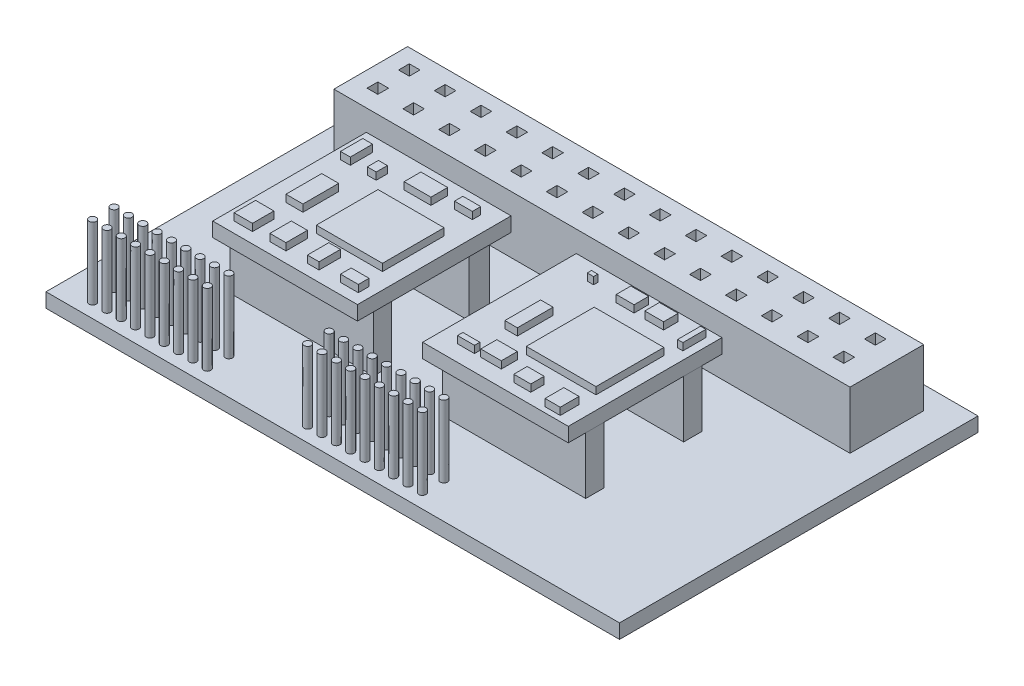
SolidWorks part; units mm, degrees
ref_plane "前视基准面" through (0, 0, 0) normal (0, 0, 1) x (1, 0, 0)
ref_plane "上视基准面" through (0, 0, 0) normal (0, 1, 0) x (1, 0, 0)
ref_plane "右视基准面" through (0, 0, 0) normal (1, 0, 0) x (0, 0, -1)
sketch "草图1" plane through (0, 0, 0) normal (0, 1, 0) x (1, 0, 0)
  line L1 (0, 50) -> (80, 50)
  line L2 (0, 50) -> (0, 0)
  line L3 (0, 0) -> (80, 0)
  line L4 (80, 50) -> (80, 0)
  dimension "D1" = 80
  dimension "D2" = 50
extrude "凸台-拉伸1" add sketch "草图1" along normal blind 2
sketch "草图2" plane through (0, 2, 0) normal (0, 1, 0) x (1, 0, 0)
  line L0 (10.7958, 38.9843) -> (12.2958, 38.9843)
  line L1 (3.6003, 46.8398) -> (75.5909, 46.8398)
  line L2 (3.6003, 46.8398) -> (3.6003, 36.5555)
  line L3 (3.6003, 36.5555) -> (75.5909, 36.5555)
  line L4 (75.5909, 46.8398) -> (75.5909, 36.5555)
  line L5 (5.7958, 44.8754) -> (7.2958, 44.8754)
  line L6 (5.7958, 44.8754) -> (5.7958, 43.3754)
  line L7 (5.7958, 43.3754) -> (7.2958, 43.3754)
  line L8 (7.2958, 44.8754) -> (7.2958, 43.3754)
  line L9 (5.7958, 40.4843) -> (7.2958, 40.4843)
  line L10 (5.7958, 40.4843) -> (5.7958, 38.9843)
  line L11 (5.7958, 38.9843) -> (7.2958, 38.9843)
  line L12 (7.2958, 40.4843) -> (7.2958, 38.9843)
  line L13 (10.7958, 40.4843) -> (10.7958, 38.9843)
  line L14 (10.7958, 40.4843) -> (12.2958, 40.4843)
  line L15 (12.2958, 40.4843) -> (12.2958, 38.9843)
  line L16 (10.7958, 43.3754) -> (12.2958, 43.3754)
  line L17 (12.2958, 44.8754) -> (12.2958, 43.3754)
  line L18 (10.7958, 44.8754) -> (12.2958, 44.8754)
  line L19 (10.7958, 44.8754) -> (10.7958, 43.3754)
  line L20 (15.7958, 38.9843) -> (17.2958, 38.9843)
  line L21 (15.7958, 40.4843) -> (15.7958, 38.9843)
  line L22 (15.7958, 40.4843) -> (17.2958, 40.4843)
  line L23 (17.2958, 40.4843) -> (17.2958, 38.9843)
  line L24 (15.7958, 43.3754) -> (17.2958, 43.3754)
  line L25 (17.2958, 44.8754) -> (17.2958, 43.3754)
  line L26 (15.7958, 44.8754) -> (17.2958, 44.8754)
  line L27 (15.7958, 44.8754) -> (15.7958, 43.3754)
  line L28 (20.7958, 38.9843) -> (22.2958, 38.9843)
  line L29 (20.7958, 40.4843) -> (20.7958, 38.9843)
  line L30 (20.7958, 40.4843) -> (22.2958, 40.4843)
  line L31 (22.2958, 40.4843) -> (22.2958, 38.9843)
  line L32 (20.7958, 43.3754) -> (22.2958, 43.3754)
  line L33 (22.2958, 44.8754) -> (22.2958, 43.3754)
  line L34 (20.7958, 44.8754) -> (22.2958, 44.8754)
  line L35 (20.7958, 44.8754) -> (20.7958, 43.3754)
  line L36 (25.7958, 38.9843) -> (27.2958, 38.9843)
  line L37 (25.7958, 40.4843) -> (25.7958, 38.9843)
  line L38 (25.7958, 40.4843) -> (27.2958, 40.4843)
  line L39 (27.2958, 40.4843) -> (27.2958, 38.9843)
  line L40 (25.7958, 43.3754) -> (27.2958, 43.3754)
  line L41 (27.2958, 44.8754) -> (27.2958, 43.3754)
  line L42 (25.7958, 44.8754) -> (27.2958, 44.8754)
  line L43 (25.7958, 44.8754) -> (25.7958, 43.3754)
  line L44 (30.7958, 38.9843) -> (32.2958, 38.9843)
  line L45 (30.7958, 40.4843) -> (30.7958, 38.9843)
  line L46 (30.7958, 40.4843) -> (32.2958, 40.4843)
  line L47 (32.2958, 40.4843) -> (32.2958, 38.9843)
  line L48 (30.7958, 43.3754) -> (32.2958, 43.3754)
  line L49 (32.2958, 44.8754) -> (32.2958, 43.3754)
  line L50 (30.7958, 44.8754) -> (32.2958, 44.8754)
  line L51 (30.7958, 44.8754) -> (30.7958, 43.3754)
  line L52 (35.7958, 38.9843) -> (37.2958, 38.9843)
  line L53 (35.7958, 40.4843) -> (35.7958, 38.9843)
  line L54 (35.7958, 40.4843) -> (37.2958, 40.4843)
  line L55 (37.2958, 40.4843) -> (37.2958, 38.9843)
  line L56 (35.7958, 43.3754) -> (37.2958, 43.3754)
  line L57 (37.2958, 44.8754) -> (37.2958, 43.3754)
  line L58 (35.7958, 44.8754) -> (37.2958, 44.8754)
  line L59 (35.7958, 44.8754) -> (35.7958, 43.3754)
  line L60 (40.7958, 38.9843) -> (42.2958, 38.9843)
  line L61 (40.7958, 40.4843) -> (40.7958, 38.9843)
  line L62 (40.7958, 40.4843) -> (42.2958, 40.4843)
  line L63 (42.2958, 40.4843) -> (42.2958, 38.9843)
  line L64 (40.7958, 43.3754) -> (42.2958, 43.3754)
  line L65 (42.2958, 44.8754) -> (42.2958, 43.3754)
  line L66 (40.7958, 44.8754) -> (42.2958, 44.8754)
  line L67 (40.7958, 44.8754) -> (40.7958, 43.3754)
  line L68 (45.7958, 38.9843) -> (47.2958, 38.9843)
  line L69 (45.7958, 40.4843) -> (45.7958, 38.9843)
  line L70 (45.7958, 40.4843) -> (47.2958, 40.4843)
  line L71 (47.2958, 40.4843) -> (47.2958, 38.9843)
  line L72 (45.7958, 43.3754) -> (47.2958, 43.3754)
  line L73 (47.2958, 44.8754) -> (47.2958, 43.3754)
  line L74 (45.7958, 44.8754) -> (47.2958, 44.8754)
  line L75 (45.7958, 44.8754) -> (45.7958, 43.3754)
  line L76 (50.7958, 38.9843) -> (52.2958, 38.9843)
  line L77 (50.7958, 40.4843) -> (50.7958, 38.9843)
  line L78 (50.7958, 40.4843) -> (52.2958, 40.4843)
  line L79 (52.2958, 40.4843) -> (52.2958, 38.9843)
  line L80 (50.7958, 43.3754) -> (52.2958, 43.3754)
  line L81 (52.2958, 44.8754) -> (52.2958, 43.3754)
  line L82 (50.7958, 44.8754) -> (52.2958, 44.8754)
  line L83 (50.7958, 44.8754) -> (50.7958, 43.3754)
  line L84 (55.7958, 38.9843) -> (57.2958, 38.9843)
  line L85 (55.7958, 40.4843) -> (55.7958, 38.9843)
  line L86 (55.7958, 40.4843) -> (57.2958, 40.4843)
  line L87 (57.2958, 40.4843) -> (57.2958, 38.9843)
  line L88 (55.7958, 43.3754) -> (57.2958, 43.3754)
  line L89 (57.2958, 44.8754) -> (57.2958, 43.3754)
  line L90 (55.7958, 44.8754) -> (57.2958, 44.8754)
  line L91 (55.7958, 44.8754) -> (55.7958, 43.3754)
  line L92 (60.7958, 38.9843) -> (62.2958, 38.9843)
  line L93 (60.7958, 40.4843) -> (60.7958, 38.9843)
  line L94 (60.7958, 40.4843) -> (62.2958, 40.4843)
  line L95 (62.2958, 40.4843) -> (62.2958, 38.9843)
  line L96 (60.7958, 43.3754) -> (62.2958, 43.3754)
  line L97 (62.2958, 44.8754) -> (62.2958, 43.3754)
  line L98 (60.7958, 44.8754) -> (62.2958, 44.8754)
  line L99 (60.7958, 44.8754) -> (60.7958, 43.3754)
  line L100 (65.7958, 38.9843) -> (67.2958, 38.9843)
  line L101 (65.7958, 40.4843) -> (65.7958, 38.9843)
  line L102 (65.7958, 40.4843) -> (67.2958, 40.4843)
  line L103 (67.2958, 40.4843) -> (67.2958, 38.9843)
  line L104 (65.7958, 43.3754) -> (67.2958, 43.3754)
  line L105 (67.2958, 44.8754) -> (67.2958, 43.3754)
  line L106 (65.7958, 44.8754) -> (67.2958, 44.8754)
  line L107 (65.7958, 44.8754) -> (65.7958, 43.3754)
  line L108 (70.7958, 38.9843) -> (72.2958, 38.9843)
  line L109 (70.7958, 40.4843) -> (70.7958, 38.9843)
  line L110 (70.7958, 40.4843) -> (72.2958, 40.4843)
  line L111 (72.2958, 40.4843) -> (72.2958, 38.9843)
  line L112 (70.7958, 43.3754) -> (72.2958, 43.3754)
  line L113 (72.2958, 44.8754) -> (72.2958, 43.3754)
  line L114 (70.7958, 44.8754) -> (72.2958, 44.8754)
  line L115 (70.7958, 44.8754) -> (70.7958, 43.3754)
  dimension "D1" = 1.5
  dimension "D2" = 1.5
  dimension "D3" = 1.5
  dimension "D4" = 1.5
  dimension "D5" = 14
extrude "凸台-拉伸2" add sketch "草图2" along normal blind 8
sketch "草图3" plane through (0, 2, 0) normal (0, 1, 0) x (1, 0, 0)
  line L0 (-5.5, 0) -> (5.5, 0) construction
  line L5 (0, -5.5) -> (0, 5.5) construction
  circle A0 centre (4.5, 2) radius 0.5
  circle A1 centre (4.5, 5) radius 0.5
  circle A2 centre (6.5, 2) radius 0.5
  circle A3 centre (6.5, 5) radius 0.5
  circle A4 centre (8.5, 2) radius 0.5
  circle A5 centre (8.5, 5) radius 0.5
  circle A6 centre (10.5, 2) radius 0.5
  circle A7 centre (10.5, 5) radius 0.5
  circle A8 centre (12.5, 2) radius 0.5
  circle A9 centre (12.5, 5) radius 0.5
  circle A10 centre (14.5, 2) radius 0.5
  circle A11 centre (14.5, 5) radius 0.5
  circle A12 centre (16.5, 2) radius 0.5
  circle A13 centre (16.5, 5) radius 0.5
  circle A14 centre (18.5, 2) radius 0.5
  circle A15 centre (18.5, 5) radius 0.5
  circle A16 centre (20.5, 2) radius 0.5
  circle A17 centre (20.5, 5) radius 0.5
  circle A18 centre (34.5, 2) radius 0.5
  circle A19 centre (34.5, 5) radius 0.5
  circle A20 centre (36.5, 2) radius 0.5
  circle A21 centre (36.5, 5) radius 0.5
  circle A22 centre (38.5, 2) radius 0.5
  circle A23 centre (38.5, 5) radius 0.5
  circle A24 centre (40.5, 2) radius 0.5
  circle A25 centre (40.5, 5) radius 0.5
  circle A26 centre (42.5, 2) radius 0.5
  circle A27 centre (42.5, 5) radius 0.5
  circle A28 centre (44.5, 2) radius 0.5
  circle A29 centre (44.5, 5) radius 0.5
  circle A30 centre (46.5, 2) radius 0.5
  circle A31 centre (46.5, 5) radius 0.5
  circle A32 centre (48.5, 2) radius 0.5
  circle A33 centre (48.5, 5) radius 0.5
  circle A34 centre (50.5, 2) radius 0.5
  circle A35 centre (50.5, 5) radius 0.5
  dimension "D1" = 1
  dimension "D2" = 1
  dimension "D3" = 3
  dimension "D4" = 2
  dimension "D5" = 4.5
  dimension "D6" = 9
  dimension "D7" = 2
extrude "凸台-拉伸3" add sketch "草图3" along normal blind 10
sketch "草图5" plane through (0, 2, 0) normal (0, 1, 0) x (1, 0, 0)
  line L1 (13.0214, 12.6628) -> (33.0214, 12.6628)
  line L2 (13.0214, 12.6628) -> (13.0214, 15.2028)
  line L3 (13.0214, 15.2028) -> (33.0214, 15.2028)
  line L4 (33.0214, 12.6628) -> (33.0214, 15.2028)
  line L5 (13.0214, 25.9969) -> (33.0214, 25.9969)
  line L6 (13.0214, 25.9969) -> (13.0214, 28.8632)
  line L7 (13.0214, 28.8632) -> (33.0214, 28.8632)
  line L8 (33.0214, 25.9969) -> (33.0214, 28.8632)
  line L9 (42.617, 12.6628) -> (62.617, 12.6628)
  line L10 (42.617, 12.6628) -> (42.617, 15.2028)
  line L11 (42.617, 15.2028) -> (62.617, 15.2028)
  line L12 (62.617, 12.6628) -> (62.617, 15.2028)
  line L13 (42.617, 26.3232) -> (62.617, 26.3232)
  line L14 (42.617, 26.3232) -> (42.617, 28.8632)
  line L15 (42.617, 28.8632) -> (62.617, 28.8632)
  line L16 (62.617, 26.3232) -> (62.617, 28.8632)
  dimension "D1" = 2.54
  dimension "D2" = 20
  dimension "D3" = 20
  dimension "D4" = 20
  dimension "D5" = 20
  dimension "D6" = 2.54
  dimension "D7" = 2.54
extrude "凸台-拉伸4" add sketch "草图5" along normal blind 8
sketch "草图6" plane through (0, 10, 0) normal (0, 1, 0) x (1, 0, 0)
  line L1 (13.0825, 10.1705) -> (33.2706, 10.1705)
  line L2 (13.0825, 10.1705) -> (13.0825, 31.6047)
  line L3 (13.0825, 31.6047) -> (33.2706, 31.6047)
  line L4 (33.2706, 10.1705) -> (33.2706, 31.6047)
  line L5 (42.3677, 10.1705) -> (62.6805, 10.1705)
  line L6 (42.3677, 10.1705) -> (42.3677, 31.6047)
  line L7 (42.3677, 31.6047) -> (62.6805, 31.6047)
  line L8 (62.6805, 10.1705) -> (62.6805, 31.6047)
extrude "凸台-拉伸5" add sketch "草图6" along normal blind 2
sketch "草图7" plane through (0, 12, 0) normal (0, 1, 0) x (1, 0, 0)
  line L1 (15.9488, 17.5229) -> (18.3165, 17.5229)
  line L2 (15.9488, 17.5229) -> (15.9488, 22.5076)
  line L3 (15.9488, 22.5076) -> (18.3165, 22.5076)
  line L4 (18.3165, 17.5229) -> (18.3165, 22.5076)
  line L5 (46.4801, 17.5229) -> (48.2248, 17.5229)
  line L6 (46.4801, 17.5229) -> (46.4801, 22.5076)
  line L7 (46.4801, 22.5076) -> (48.2248, 22.5076)
  line L8 (48.2248, 17.5229) -> (48.2248, 22.5076)
  line L9 (21.8058, 15.9029) -> (31.0275, 15.9029)
  line L10 (21.8058, 15.9029) -> (21.8058, 24.5015)
  line L11 (21.8058, 24.5015) -> (31.0275, 24.5015)
  line L12 (31.0275, 15.9029) -> (31.0275, 24.5015)
  line L13 (51.091, 15.9029) -> (60.8112, 15.9029)
  line L14 (51.091, 15.9029) -> (51.091, 25.3739)
  line L15 (51.091, 25.3739) -> (60.8112, 25.3739)
  line L16 (60.8112, 15.9029) -> (60.8112, 25.3739)
  line L17 (14.578, 11.6659) -> (17.1326, 11.6659)
  line L18 (14.578, 11.6659) -> (14.578, 14.6567)
  line L19 (14.578, 14.6567) -> (17.1326, 14.6567)
  line L20 (17.1326, 11.6659) -> (17.1326, 14.6567)
  line L21 (19.5627, 11.6659) -> (21.8058, 11.6659)
  line L22 (19.5627, 11.6659) -> (19.5627, 14.6567)
  line L23 (19.5627, 14.6567) -> (21.8058, 14.6567)
  line L24 (21.8058, 11.6659) -> (21.8058, 14.6567)
  line L25 (24.7966, 11.6659) -> (26.4167, 11.6659)
  line L26 (24.7966, 11.6659) -> (24.7966, 14.6567)
  line L27 (24.7966, 14.6567) -> (26.4167, 14.6567)
  line L28 (26.4167, 11.6659) -> (26.4167, 14.6567)
  line L29 (29.4075, 11.6659) -> (31.8998, 11.6659)
  line L30 (29.4075, 11.6659) -> (29.4075, 13.1613)
  line L31 (29.4075, 13.1613) -> (31.8998, 13.1613)
  line L32 (31.8998, 11.6659) -> (31.8998, 13.1613)
  line L33 (14.578, 26.4954) -> (15.9488, 26.4954)
  line L34 (14.578, 26.4954) -> (14.578, 29.6109)
  line L35 (14.578, 29.6109) -> (15.9488, 29.6109)
  line L36 (15.9488, 26.4954) -> (15.9488, 29.6109)
  line L37 (18.3165, 26.4954) -> (19.5627, 26.4954)
  line L38 (18.3165, 26.4954) -> (18.3165, 28.0531)
  line L39 (18.3165, 28.0531) -> (19.5627, 28.0531)
  line L40 (19.5627, 26.4954) -> (19.5627, 28.0531)
  line L41 (22.6781, 27.2743) -> (26.4167, 27.2743)
  line L42 (22.6781, 27.2743) -> (22.6781, 29.6109)
  line L43 (22.6781, 29.6109) -> (26.4167, 29.6109)
  line L44 (26.4167, 27.2743) -> (26.4167, 29.6109)
  line L45 (28.5352, 28.4426) -> (31.0275, 28.4426)
  line L46 (28.5352, 28.4426) -> (28.5352, 29.6109)
  line L47 (28.5352, 29.6109) -> (31.0275, 29.6109)
  line L48 (31.0275, 28.4426) -> (31.0275, 29.6109)
  line L49 (46.4801, 29.0267) -> (47.3525, 29.0267)
  line L50 (46.4801, 29.0267) -> (46.4801, 29.6109)
  line L51 (46.4801, 29.6109) -> (47.3525, 29.6109)
  line L52 (47.3525, 29.0267) -> (47.3525, 29.6109)
  line L53 (51.091, 28.4426) -> (53.5833, 28.4426)
  line L54 (51.091, 28.4426) -> (51.091, 30.4832)
  line L55 (51.091, 30.4832) -> (53.5833, 30.4832)
  line L56 (53.5833, 28.4426) -> (53.5833, 30.4832)
  line L57 (55.0788, 28.4426) -> (57.6957, 28.4426)
  line L58 (55.0788, 28.4426) -> (55.0788, 30.4832)
  line L59 (55.0788, 30.4832) -> (57.6957, 30.4832)
  line L60 (57.6957, 28.4426) -> (57.6957, 30.4832)
  line L61 (60.8112, 27.2743) -> (61.5589, 27.2743)
  line L62 (60.8112, 27.2743) -> (60.8112, 30.4832)
  line L63 (60.8112, 30.4832) -> (61.5589, 30.4832)
  line L64 (61.5589, 27.2743) -> (61.5589, 30.4832)
  line L65 (44.9847, 12.4136) -> (47.3525, 12.4136)
  line L66 (44.9847, 12.4136) -> (44.9847, 13.1613)
  line L67 (44.9847, 13.1613) -> (47.3525, 13.1613)
  line L68 (47.3525, 12.4136) -> (47.3525, 13.1613)
  line L69 (48.2248, 12.4136) -> (51.091, 12.4136)
  line L70 (48.2248, 12.4136) -> (48.2248, 14.6567)
  line L71 (48.2248, 14.6567) -> (51.091, 14.6567)
  line L72 (51.091, 12.4136) -> (51.091, 14.6567)
  line L73 (53.5833, 11.6659) -> (55.9511, 11.6659)
  line L74 (53.5833, 11.6659) -> (53.5833, 13.5352)
  line L75 (53.5833, 13.5352) -> (55.9511, 13.5352)
  line L76 (55.9511, 11.6659) -> (55.9511, 13.5352)
  line L77 (58.6927, 10.9182) -> (60.8112, 10.9182)
  line L78 (58.6927, 10.9182) -> (58.6927, 13.5352)
  line L79 (58.6927, 13.5352) -> (60.8112, 13.5352)
  line L80 (60.8112, 10.9182) -> (60.8112, 13.5352)
extrude "凸台-拉伸6" add sketch "草图7" along normal blind 1
